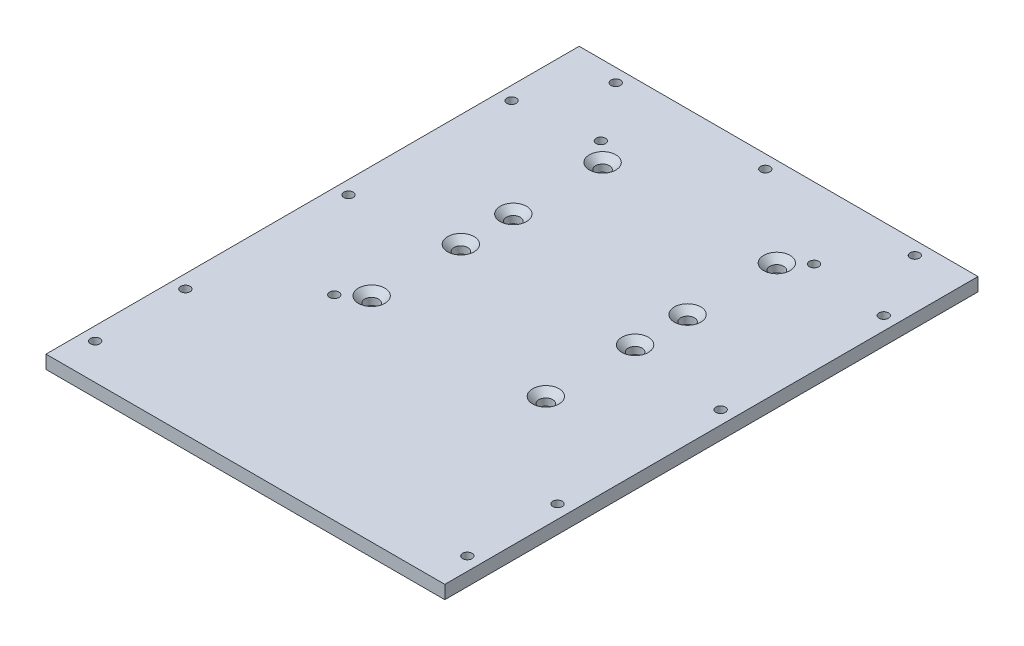
SolidWorks part; units mm, degrees
ref_plane "Front Plane" through (0, 0, 0) normal (0, 0, 1) x (1, 0, 0)
ref_plane "Top Plane" through (0, 0, 0) normal (0, 1, 0) x (1, 0, 0)
ref_plane "Right Plane" through (0, 0, 0) normal (1, 0, 0) x (0, 0, -1)
sketch "Sketch1" plane through (0, 0, 0) normal (0, 1, 0) x (1, 0, 0)
  line L1 (-94.996, 127) -> (94.996, 127)
  line L2 (-94.996, 127) -> (-94.996, -127)
  line L3 (-94.996, -127) -> (94.996, -127)
  line L4 (94.996, 127) -> (94.996, -127)
  point P4 (0, 127)
  point P6 (-94.996, 0)
  dimension "D1" = 254
  dimension "D2" = 189.992
extrude "Boss-Extrude1" add sketch "Sketch1" along normal blind 6.35
sketch "Sketch2" plane through (0, 0, 0) normal (0, 1, 0) x (1, 0, 0)
  line L0 (94.996, 127) -> (-94.996, 127) construction
  line L1 (-50.8, 93.1164) -> (50.8, 93.1164)
  line L2 (-50.8, 93.1164) -> (-50.8, -33.8836)
  line L3 (-50.8, -33.8836) -> (50.8, -33.8836)
  line L4 (50.8, 93.1164) -> (50.8, -33.8836)
  point P4 (0, 93.1164)
  point P9 (-50.8, 93.1164)
  point P10 (50.8, 93.1164)
  point P11 (-50.8, -33.8836)
  dimension "D1" = 33.8836
  dimension "D2" = 127
  dimension "D3" = 101.6
sketch "Sketch3" plane through (0, 6.35, 0) normal (0, 1, 0) x (1, 0, 0)
  line L0 (-94.996, -127) -> (94.996, -127) construction
  line L1 (-94.996, 127) -> (-94.996, -127) construction
  line L2 (94.996, 127) -> (-94.996, 127) construction
  circle A0 centre (-88.646, -109.9312) radius 2.2479
  circle A1 centre (-88.646, -66.9544) radius 2.2479
  circle A3 centre (-88.646, 10.7442) radius 2.2479
  circle A4 centre (-88.646, 88.4428) radius 2.2479
  circle A5 centre (-50.8, 93.1164) radius 2.2479
  circle A6 centre (-71.247, 120.65) radius 2.2479
  circle A7 centre (0, 120.65) radius 2.2479
  dimension "D1" = 17.0688
  dimension "D2" = 6.35
  dimension "D3" = 4.4958
  dimension "D4" = 42.9768
  dimension "D5" = 77.6986
  dimension "D6" = 77.6986
  dimension "D7" = 6.35
  dimension "D8" = 23.749
extrude "Cut-Extrude1" cut sketch "Sketch3" against normal through all
mirror "Mirror1" about plane through (0, 0, 0) normal (1, 0, 0) of "Cut-Extrude1"
sketch "Sketch4" plane through (0, 6.35, 0) normal (0, 1, 0) x (1, 0, 0)
  circle A0 centre (-50.8, -33.8836) radius 2.2479
  circle A1 centre (-88.646, -66.9544) radius 2.2479 construction
extrude "Cut-Extrude2" cut sketch "Sketch4" against normal through all
sketch "Sketch5" plane through (0, 6.35, 0) normal (0, 1, 0) x (1, 0, 0)
  line L0 (-94.996, -127) -> (94.996, -127) construction
  line L1 (-94.996, 127) -> (-94.996, -127) construction
  point P0 (-41.5036, -25.3746)
  point P1 (-41.5036, 17.145)
  point P2 (-41.5036, 42.1386)
  point P3 (-41.5036, 84.6582)
  dimension "D1" = 101.6254
  dimension "D2" = 42.5196
  dimension "D3" = 24.9936
  dimension "D4" = 42.5196
  dimension "D5" = 53.4924
hole_wizard "CSK for M6 Countersunk Flat Head Screw1" positions "Sketch6" profile "Sketch7" countersink size "M6" standard "ISO"
sketch "Sketch6" plane through (0, 6.35, 0) normal (0, 1, 0) x (1, 0, 0)
  point P0 (-41.5036, 17.145)
  point P3 (-41.5036, -25.3746)
  point P6 (-41.5036, 42.1386)
  point P9 (-41.5036, 84.6582)
sketch "Sketch7" plane through (-41.5036, 6.35, -17.145) normal (1, 0, 0) x (0, 0, 1)
  line L0 (0, 0) -> (0, 46.984)
  line L1 (0, 46.984) -> (3.302, 45)
  line L2 (3.302, 45) -> (3.302, 2.9972)
  line L3 (3.302, 2.9972) -> (6.2992, 0)
  line L5 (6.2992, 0) -> (0, 0)
  line L6 (-3.302, 2.9972) -> (-6.2992, 0) construction
  line L10 (0, 46.984) -> (-3.302, 45) construction
  line L11 (0, -6.35) -> (0, 107.95) construction
  dimension "Hole Dia." = 6.604
  dimension "Hole Depth" = 45
  dimension "Near C'Sink Dia." = 12.5984
  dimension "Near C'Sink Angle" = 90
  dimension "Drill Angle" = 118
mirror "Mirror2" about plane through (0, 0, 0) normal (1, 0, 0) of "CSK for M6 Countersunk Flat Head Screw1"
